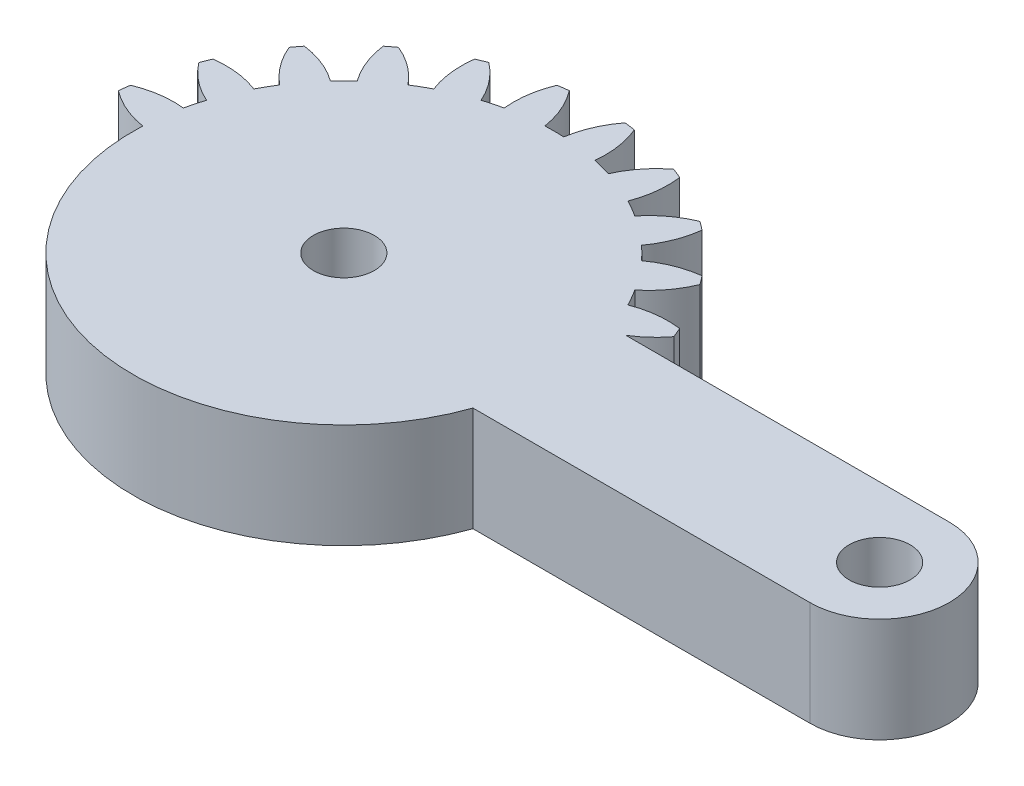
SolidWorks part; units mm, degrees
ref_plane "Front Plane" through (0, 0, 0) normal (0, 0, 1) x (1, 0, 0)
ref_plane "Top Plane" through (0, 0, 0) normal (0, 1, 0) x (1, 0, 0)
ref_plane "Right Plane" through (0, 0, 0) normal (1, 0, 0) x (0, 0, -1)
sketch "Sketch1" plane through (0, 0, 0) normal (0, 1, 0) x (1, 0, 0)
  line L0 (20.6437, 4) -> (2.0816, 4)
  line L1 (2.0816, -4) -> (20.6437, -4)
  arc A0 (2.0816, 4) -> (3.5217, 5.3071) centre (-0.7683, 8.5867) ccw
  arc A1 (3.5217, 5.3071) -> (3.2829, 5.8838) centre (-10.1063, 0) ccw
  arc A2 (3.2829, 5.8838) -> (0.6271, 5.5703) centre (2.5684, 0.5313) ccw
  arc A3 (0.6271, 5.5703) -> (0.0844, 6.5103) centre (-10.1063, 0) ccw
  arc A4 (0.0844, 6.5103) -> (1.6838, 8.6535) centre (-3.3089, 10.711) ccw
  arc A5 (1.6838, 8.6535) -> (1.3038, 9.1487) centre (-10.1063, 0) ccw
  arc A6 (1.3038, 9.1487) -> (-1.1803, 8.1585) centre (1.999, 3.7936) ccw
  arc A7 (-1.1803, 8.1585) -> (-1.9479, 8.926) centre (-10.1063, 0) ccw
  arc A8 (-1.9479, 8.926) -> (-0.9576, 11.4102) centre (-6.3127, 12.1053) ccw
  arc A9 (-0.9576, 11.4102) -> (-1.4528, 11.7901) centre (-10.1063, 0) ccw
  arc A10 (-1.4528, 11.7901) -> (-3.596, 10.1907) centre (0.6046, 6.7975) ccw
  arc A11 (-3.596, 10.1907) -> (-4.5361, 10.7334) centre (-10.1063, 0) ccw
  arc A12 (-4.5361, 10.7334) -> (-4.2225, 13.3892) centre (-9.5751, 12.6747) ccw
  arc A13 (-4.2225, 13.3892) -> (-4.7992, 13.6281) centre (-10.1063, 0) ccw
  arc A14 (-4.7992, 13.6281) -> (-6.4554, 11.5285) centre (-1.5196, 9.3381) ccw
  arc A15 (-6.4554, 11.5285) -> (-7.5039, 11.8094) centre (-10.1063, 0) ccw
  arc A16 (-7.5039, 11.8094) -> (-7.8884, 14.4558) centre (-12.8736, 12.3803) ccw
  arc A17 (-7.8884, 14.4558) -> (-8.5072, 14.5373) centre (-10.1063, 0) ccw
  arc A18 (-8.5072, 14.5373) -> (-9.5636, 12.0806) centre (-4.2291, 11.2423) ccw
  arc A19 (-9.5636, 12.0806) -> (-10.6491, 12.0806) centre (-10.1063, 0) ccw
  arc A20 (-10.6491, 12.0806) -> (-11.7054, 14.5373) centre (-15.9836, 11.2423) ccw
  arc A21 (-11.7054, 14.5373) -> (-12.3243, 14.4558) centre (-10.1063, 0) ccw
  arc A22 (-12.3243, 14.4558) -> (-12.7088, 11.8094) centre (-7.3391, 12.3803) ccw
  arc A23 (-12.7088, 11.8094) -> (-13.7573, 11.5285) centre (-10.1063, 0) ccw
  arc A24 (-13.7573, 11.5285) -> (-15.4135, 13.6281) centre (-18.6931, 9.3381) ccw
  arc A25 (-15.4135, 13.6281) -> (-15.9901, 13.3892) centre (-10.1063, 0) ccw
  arc A26 (-15.9901, 13.3892) -> (-15.6766, 10.7334) centre (-10.6376, 12.6747) ccw
  arc A27 (-15.6766, 10.7334) -> (-16.6166, 10.1907) centre (-10.1063, 0) ccw
  arc A28 (-16.6166, 10.1907) -> (-18.7599, 11.7901) centre (-20.8173, 6.7975) ccw
  arc A29 (-18.7599, 11.7901) -> (-19.255, 11.4102) centre (-10.1063, 0) ccw
  arc A30 (-19.255, 11.4102) -> (-18.2648, 8.926) centre (-13.9, 12.1053) ccw
  arc A31 (-18.2648, 8.926) -> (-19.0324, 8.1585) centre (-10.1063, 0) ccw
  arc A32 (-19.0324, 8.1585) -> (-21.5165, 9.1487) centre (-22.2117, 3.7936) ccw
  arc A33 (-21.5165, 9.1487) -> (-21.8965, 8.6535) centre (-10.1063, 0) ccw
  arc A34 (-21.8965, 8.6535) -> (-20.2971, 6.5103) centre (-16.9038, 10.711) ccw
  arc A35 (-20.2971, 6.5103) -> (-20.8398, 5.5703) centre (-10.1063, 0) ccw
  arc A36 (-20.8398, 5.5703) -> (-23.4956, 5.8838) centre (-22.7811, 0.5313) ccw
  arc A37 (-23.4956, 5.8838) -> (-23.7344, 5.3071) centre (-10.1063, 0) ccw
  arc A38 (-23.7344, 5.3071) -> (-21.6348, 3.6509) centre (-19.4444, 8.5867) ccw
  arc A39 (-21.6348, 3.6509) -> (-21.9157, 2.6025) centre (-10.1063, 0) ccw
  arc A40 (-21.9157, 2.6025) -> (-24.5622, 2.2179) centre (-22.4867, -2.7673) ccw
  arc A41 (-24.5622, 2.2179) -> (-24.6437, 1.5991) centre (-10.1063, 0) ccw
  arc A42 (-24.6437, 1.5991) -> (-22.1869, 0.5427) centre (-21.3486, 5.8773) ccw
  arc A43 (-22.1869, 0.5427) -> (-22.1869, -0.5427) centre (-10.1063, 0) ccw
  arc A44 (-22.1869, -0.5427) -> (-24.6437, -1.5991) centre (-21.3486, -5.8773) ccw
  arc A45 (-24.6437, -1.5991) -> (-24.5622, -2.2179) centre (-10.1063, 0) ccw
  arc A46 (-24.5622, -2.2179) -> (-21.9157, -2.6025) centre (-22.4867, 2.7673) ccw
  arc A47 (-21.9157, -2.6025) -> (-21.6348, -3.6509) centre (-10.1063, 0) ccw
  arc A48 (-21.6348, -3.6509) -> (-23.7344, -5.3071) centre (-19.4444, -8.5867) ccw
  arc A49 (-23.7344, -5.3071) -> (-23.4956, -5.8838) centre (-10.1063, 0) ccw
  arc A50 (-23.4956, -5.8838) -> (-20.8398, -5.5703) centre (-22.7811, -0.5313) ccw
  arc A51 (-20.8398, -5.5703) -> (-20.2971, -6.5103) centre (-10.1063, 0) ccw
  arc A52 (-20.2971, -6.5103) -> (-21.8965, -8.6535) centre (-16.9038, -10.711) ccw
  arc A53 (-21.8965, -8.6535) -> (-21.5165, -9.1487) centre (-10.1063, 0) ccw
  arc A54 (-21.5165, -9.1487) -> (-19.0324, -8.1585) centre (-22.2117, -3.7936) ccw
  arc A55 (-19.0324, -8.1585) -> (-18.2648, -8.926) centre (-10.1063, 0) ccw
  arc A56 (-18.2648, -8.926) -> (-19.255, -11.4102) centre (-13.9, -12.1053) ccw
  arc A57 (-19.255, -11.4102) -> (-18.7599, -11.7901) centre (-10.1063, 0) ccw
  arc A58 (-18.7599, -11.7901) -> (-16.6166, -10.1907) centre (-20.8173, -6.7975) ccw
  arc A59 (-16.6166, -10.1907) -> (-15.6766, -10.7334) centre (-10.1063, 0) ccw
  arc A60 (-15.6766, -10.7334) -> (-15.9901, -13.3892) centre (-10.6376, -12.6747) ccw
  arc A61 (-15.9901, -13.3892) -> (-15.4135, -13.6281) centre (-10.1063, 0) ccw
  arc A62 (-15.4135, -13.6281) -> (-13.7573, -11.5285) centre (-18.6931, -9.3381) ccw
  arc A63 (-13.7573, -11.5285) -> (-12.7088, -11.8094) centre (-10.1063, 0) ccw
  arc A64 (-12.7088, -11.8094) -> (-12.3243, -14.4558) centre (-7.3391, -12.3803) ccw
  arc A65 (-12.3243, -14.4558) -> (-11.7054, -14.5373) centre (-10.1063, 0) ccw
  arc A66 (-11.7054, -14.5373) -> (-10.6491, -12.0806) centre (-15.9836, -11.2423) ccw
  arc A67 (-10.6491, -12.0806) -> (-9.5636, -12.0806) centre (-10.1063, 0) ccw
  arc A68 (-9.5636, -12.0806) -> (-8.5072, -14.5373) centre (-4.2291, -11.2423) ccw
  arc A69 (-8.5072, -14.5373) -> (-7.8884, -14.4558) centre (-10.1063, 0) ccw
  arc A70 (-7.8884, -14.4558) -> (-7.5039, -11.8094) centre (-12.8736, -12.3803) ccw
  arc A71 (-7.5039, -11.8094) -> (-6.4554, -11.5285) centre (-10.1063, 0) ccw
  arc A72 (-6.4554, -11.5285) -> (-4.7992, -13.6281) centre (-1.5196, -9.3381) ccw
  arc A73 (-4.7992, -13.6281) -> (-4.2225, -13.3892) centre (-10.1063, 0) ccw
  arc A74 (-4.2225, -13.3892) -> (-4.5361, -10.7334) centre (-9.5751, -12.6747) ccw
  arc A75 (-4.5361, -10.7334) -> (-3.596, -10.1907) centre (-10.1063, 0) ccw
  arc A76 (-3.596, -10.1907) -> (-1.4528, -11.7901) centre (0.6046, -6.7975) ccw
  arc A77 (-1.4528, -11.7901) -> (-0.9576, -11.4102) centre (-10.1063, 0) ccw
  arc A78 (-0.9576, -11.4102) -> (-1.9479, -8.926) centre (-6.3127, -12.1053) ccw
  arc A79 (-1.9479, -8.926) -> (-1.1803, -8.1585) centre (-10.1063, 0) ccw
  arc A80 (-1.1803, -8.1585) -> (1.3038, -9.1487) centre (1.999, -3.7936) ccw
  arc A81 (1.3038, -9.1487) -> (1.6838, -8.6535) centre (-10.1063, 0) ccw
  arc A82 (1.6838, -8.6535) -> (0.0844, -6.5103) centre (-3.3089, -10.711) ccw
  arc A83 (0.0844, -6.5103) -> (0.6271, -5.5703) centre (-10.1063, 0) ccw
  arc A84 (0.6271, -5.5703) -> (3.2829, -5.8838) centre (2.5684, -0.5313) ccw
  arc A85 (3.2829, -5.8838) -> (3.5217, -5.3071) centre (-10.1063, 0) ccw
  arc A86 (3.5217, -5.3071) -> (2.0816, -4) centre (-0.7683, -8.5867) ccw
  arc A87 (20.6437, -4) -> (20.6437, 4) centre (20.6437, 0) ccw
  circle A88 centre (-10.1063, 0) radius 1.75
  circle A89 centre (20.6437, 0) radius 1.75
  dimension "D1" = 3.5
  dimension "D2" = 3.5
extrude "Boss-Extrude1" add sketch "Sketch1" along normal blind 4
sketch "Sketch2" plane through (0, 4, 0) normal (0, 1, 0) x (1, 0, 0)
  line L0 (2.0816, -4) -> (1.3057, -4)
  line L2 (20.6437, 4) -> (2.0816, 4)
  line L3 (2.0816, -4) -> (20.6437, -4)
  line L4 (20.6437, 4) -> (2.0816, 4)
  line L5 (2.0816, -4) -> (20.6437, -4)
  circle A0 centre (-10.1063, 0) radius 12.0927
  arc A88 (20.6437, -4) -> (20.6437, 4) centre (20.6437, 0) ccw
  arc A89 (2.0816, 4) -> (3.5217, 5.3071) centre (-0.7683, 8.5867) ccw
  arc A90 (3.5217, 5.3071) -> (3.2829, 5.8838) centre (-10.1063, 0) ccw
  arc A91 (3.2829, 5.8838) -> (0.6271, 5.5703) centre (2.5684, 0.5313) ccw
  arc A92 (0.6271, 5.5703) -> (0.0844, 6.5103) centre (-10.1063, 0) ccw
  arc A93 (0.0844, 6.5103) -> (1.6838, 8.6535) centre (-3.3089, 10.711) ccw
  arc A94 (1.6838, 8.6535) -> (1.3038, 9.1487) centre (-10.1063, 0) ccw
  arc A95 (1.3038, 9.1487) -> (-1.1803, 8.1585) centre (1.999, 3.7936) ccw
  arc A96 (-1.1803, 8.1585) -> (-1.9479, 8.926) centre (-10.1063, 0) ccw
  arc A97 (-1.9479, 8.926) -> (-0.9576, 11.4102) centre (-6.3127, 12.1053) ccw
  arc A98 (-0.9576, 11.4102) -> (-1.4528, 11.7901) centre (-10.1063, 0) ccw
  arc A99 (-1.4528, 11.7901) -> (-3.596, 10.1907) centre (0.6046, 6.7975) ccw
  arc A100 (-3.596, 10.1907) -> (-4.5361, 10.7334) centre (-10.1063, 0) ccw
  arc A101 (-4.5361, 10.7334) -> (-4.2225, 13.3892) centre (-9.5751, 12.6747) ccw
  arc A102 (-4.2225, 13.3892) -> (-4.7992, 13.6281) centre (-10.1063, 0) ccw
  arc A103 (-4.7992, 13.6281) -> (-6.4554, 11.5285) centre (-1.5196, 9.3381) ccw
  arc A104 (-6.4554, 11.5285) -> (-7.5039, 11.8094) centre (-10.1063, 0) ccw
  arc A105 (-7.5039, 11.8094) -> (-7.8884, 14.4558) centre (-12.8736, 12.3803) ccw
  arc A106 (-7.8884, 14.4558) -> (-8.5072, 14.5373) centre (-10.1063, 0) ccw
  arc A107 (-8.5072, 14.5373) -> (-9.5636, 12.0806) centre (-4.2291, 11.2423) ccw
  arc A108 (-9.5636, 12.0806) -> (-10.6491, 12.0806) centre (-10.1063, 0) ccw
  arc A109 (-10.6491, 12.0806) -> (-11.7054, 14.5373) centre (-15.9836, 11.2423) ccw
  arc A110 (-11.7054, 14.5373) -> (-12.3243, 14.4558) centre (-10.1063, 0) ccw
  arc A111 (-12.3243, 14.4558) -> (-12.7088, 11.8094) centre (-7.3391, 12.3803) ccw
  arc A112 (-12.7088, 11.8094) -> (-13.7573, 11.5285) centre (-10.1063, 0) ccw
  arc A113 (-13.7573, 11.5285) -> (-15.4135, 13.6281) centre (-18.6931, 9.3381) ccw
  arc A114 (-15.4135, 13.6281) -> (-15.9901, 13.3892) centre (-10.1063, 0) ccw
  arc A115 (-15.9901, 13.3892) -> (-15.6766, 10.7334) centre (-10.6376, 12.6747) ccw
  arc A116 (-15.6766, 10.7334) -> (-16.6166, 10.1907) centre (-10.1063, 0) ccw
  arc A117 (-16.6166, 10.1907) -> (-18.7599, 11.7901) centre (-20.8173, 6.7975) ccw
  arc A118 (-18.7599, 11.7901) -> (-19.255, 11.4102) centre (-10.1063, 0) ccw
  arc A119 (-19.255, 11.4102) -> (-18.2648, 8.926) centre (-13.9, 12.1053) ccw
  arc A120 (-18.2648, 8.926) -> (-19.0324, 8.1585) centre (-10.1063, 0) ccw
  arc A121 (-19.0324, 8.1585) -> (-21.5165, 9.1487) centre (-22.2117, 3.7936) ccw
  arc A122 (-21.5165, 9.1487) -> (-21.8965, 8.6535) centre (-10.1063, 0) ccw
  arc A123 (-21.8965, 8.6535) -> (-20.2971, 6.5103) centre (-16.9038, 10.711) ccw
  arc A124 (-20.2971, 6.5103) -> (-20.8398, 5.5703) centre (-10.1063, 0) ccw
  arc A125 (-20.8398, 5.5703) -> (-23.4956, 5.8838) centre (-22.7811, 0.5313) ccw
  arc A126 (-23.4956, 5.8838) -> (-23.7344, 5.3071) centre (-10.1063, 0) ccw
  arc A127 (-23.7344, 5.3071) -> (-21.6348, 3.6509) centre (-19.4444, 8.5867) ccw
  arc A128 (-21.6348, 3.6509) -> (-21.9157, 2.6025) centre (-10.1063, 0) ccw
  arc A129 (-21.9157, 2.6025) -> (-24.5622, 2.2179) centre (-22.4867, -2.7673) ccw
  arc A130 (-24.5622, 2.2179) -> (-24.6437, 1.5991) centre (-10.1063, 0) ccw
  arc A131 (-24.6437, 1.5991) -> (-22.1869, 0.5427) centre (-21.3486, 5.8773) ccw
  arc A132 (-22.1869, 0.5427) -> (-22.1869, -0.5427) centre (-10.1063, 0) ccw
  arc A133 (-22.1869, -0.5427) -> (-24.6437, -1.5991) centre (-21.3486, -5.8773) ccw
  arc A134 (-24.6437, -1.5991) -> (-24.5622, -2.2179) centre (-10.1063, 0) ccw
  arc A135 (-24.5622, -2.2179) -> (-21.9157, -2.6025) centre (-22.4867, 2.7673) ccw
  arc A136 (-21.9157, -2.6025) -> (-21.6348, -3.6509) centre (-10.1063, 0) ccw
  arc A137 (-21.6348, -3.6509) -> (-23.7344, -5.3071) centre (-19.4444, -8.5867) ccw
  arc A138 (-23.7344, -5.3071) -> (-23.4956, -5.8838) centre (-10.1063, 0) ccw
  arc A139 (-23.4956, -5.8838) -> (-20.8398, -5.5703) centre (-22.7811, -0.5313) ccw
  arc A140 (-20.8398, -5.5703) -> (-20.2971, -6.5103) centre (-10.1063, 0) ccw
  arc A141 (-20.2971, -6.5103) -> (-21.8965, -8.6535) centre (-16.9038, -10.711) ccw
  arc A142 (-21.8965, -8.6535) -> (-21.5165, -9.1487) centre (-10.1063, 0) ccw
  arc A143 (-21.5165, -9.1487) -> (-19.0324, -8.1585) centre (-22.2117, -3.7936) ccw
  arc A144 (-19.0324, -8.1585) -> (-18.2648, -8.926) centre (-10.1063, 0) ccw
  arc A145 (-18.2648, -8.926) -> (-19.255, -11.4102) centre (-13.9, -12.1053) ccw
  arc A146 (-19.255, -11.4102) -> (-18.7599, -11.7901) centre (-10.1063, 0) ccw
  arc A147 (-18.7599, -11.7901) -> (-16.6166, -10.1907) centre (-20.8173, -6.7975) ccw
  arc A148 (-16.6166, -10.1907) -> (-15.6766, -10.7334) centre (-10.1063, 0) ccw
  arc A149 (-15.6766, -10.7334) -> (-15.9901, -13.3892) centre (-10.6376, -12.6747) ccw
  arc A150 (-15.9901, -13.3892) -> (-15.4135, -13.6281) centre (-10.1063, 0) ccw
  arc A151 (-15.4135, -13.6281) -> (-13.7573, -11.5285) centre (-18.6931, -9.3381) ccw
  arc A152 (-13.7573, -11.5285) -> (-12.7088, -11.8094) centre (-10.1063, 0) ccw
  arc A153 (-12.7088, -11.8094) -> (-12.3243, -14.4558) centre (-7.3391, -12.3803) ccw
  arc A154 (-12.3243, -14.4558) -> (-11.7054, -14.5373) centre (-10.1063, 0) ccw
  arc A155 (-11.7054, -14.5373) -> (-10.6491, -12.0806) centre (-15.9836, -11.2423) ccw
  arc A156 (-10.6491, -12.0806) -> (-9.5636, -12.0806) centre (-10.1063, 0) ccw
  arc A157 (-9.5636, -12.0806) -> (-8.5072, -14.5373) centre (-4.2291, -11.2423) ccw
  arc A158 (-8.5072, -14.5373) -> (-7.8884, -14.4558) centre (-10.1063, 0) ccw
  arc A159 (-7.8884, -14.4558) -> (-7.5039, -11.8094) centre (-12.8736, -12.3803) ccw
  arc A160 (-7.5039, -11.8094) -> (-6.4554, -11.5285) centre (-10.1063, 0) ccw
  arc A161 (-6.4554, -11.5285) -> (-4.7992, -13.6281) centre (-1.5196, -9.3381) ccw
  arc A162 (-4.7992, -13.6281) -> (-4.2225, -13.3892) centre (-10.1063, 0) ccw
  arc A163 (-4.2225, -13.3892) -> (-4.5361, -10.7334) centre (-9.5751, -12.6747) ccw
  arc A164 (-4.5361, -10.7334) -> (-3.596, -10.1907) centre (-10.1063, 0) ccw
  arc A165 (-3.596, -10.1907) -> (-1.4528, -11.7901) centre (0.6046, -6.7975) ccw
  arc A166 (-1.4528, -11.7901) -> (-0.9576, -11.4102) centre (-10.1063, 0) ccw
  arc A167 (-0.9576, -11.4102) -> (-1.9479, -8.926) centre (-6.3127, -12.1053) ccw
  arc A168 (-1.9479, -8.926) -> (-1.1803, -8.1585) centre (-10.1063, 0) ccw
  arc A169 (-1.1803, -8.1585) -> (1.3038, -9.1487) centre (1.999, -3.7936) ccw
  arc A170 (1.3038, -9.1487) -> (1.6838, -8.6535) centre (-10.1063, 0) ccw
  arc A171 (1.6838, -8.6535) -> (0.0844, -6.5103) centre (-3.3089, -10.711) ccw
  arc A172 (0.0844, -6.5103) -> (0.6271, -5.5703) centre (-10.1063, 0) ccw
  arc A173 (0.6271, -5.5703) -> (3.2829, -5.8838) centre (2.5684, -0.5313) ccw
  arc A174 (3.2829, -5.8838) -> (3.5217, -5.3071) centre (-10.1063, 0) ccw
  arc A175 (3.5217, -5.3071) -> (2.0816, -4) centre (-0.7683, -8.5867) ccw
  arc A176 (20.6437, -4) -> (20.6437, 4) centre (20.6437, 0) ccw
  arc A177 (2.0816, 4) -> (3.5217, 5.3071) centre (-0.7683, 8.5867) ccw
  arc A178 (3.5217, 5.3071) -> (3.2829, 5.8838) centre (-10.1063, 0) ccw
  arc A179 (3.2829, 5.8838) -> (0.6271, 5.5703) centre (2.5684, 0.5313) ccw
  arc A180 (0.6271, 5.5703) -> (0.0844, 6.5103) centre (-10.1063, 0) ccw
  arc A181 (0.0844, 6.5103) -> (1.6838, 8.6535) centre (-3.3089, 10.711) ccw
  arc A182 (1.6838, 8.6535) -> (1.3038, 9.1487) centre (-10.1063, 0) ccw
  arc A183 (1.3038, 9.1487) -> (-1.1803, 8.1585) centre (1.999, 3.7936) ccw
  arc A184 (-1.1803, 8.1585) -> (-1.9479, 8.926) centre (-10.1063, 0) ccw
  arc A185 (-1.9479, 8.926) -> (-0.9576, 11.4102) centre (-6.3127, 12.1053) ccw
  arc A186 (-0.9576, 11.4102) -> (-1.4528, 11.7901) centre (-10.1063, 0) ccw
  arc A187 (-1.4528, 11.7901) -> (-3.596, 10.1907) centre (0.6046, 6.7975) ccw
  arc A188 (-3.596, 10.1907) -> (-4.5361, 10.7334) centre (-10.1063, 0) ccw
  arc A189 (-4.5361, 10.7334) -> (-4.2225, 13.3892) centre (-9.5751, 12.6747) ccw
  arc A190 (-4.2225, 13.3892) -> (-4.7992, 13.6281) centre (-10.1063, 0) ccw
  arc A191 (-4.7992, 13.6281) -> (-6.4554, 11.5285) centre (-1.5196, 9.3381) ccw
  arc A192 (-6.4554, 11.5285) -> (-7.5039, 11.8094) centre (-10.1063, 0) ccw
  arc A193 (-7.5039, 11.8094) -> (-7.8884, 14.4558) centre (-12.8736, 12.3803) ccw
  arc A194 (-7.8884, 14.4558) -> (-8.5072, 14.5373) centre (-10.1063, 0) ccw
  arc A195 (-8.5072, 14.5373) -> (-9.5636, 12.0806) centre (-4.2291, 11.2423) ccw
  arc A196 (-9.5636, 12.0806) -> (-10.6491, 12.0806) centre (-10.1063, 0) ccw
  arc A197 (-10.6491, 12.0806) -> (-11.7054, 14.5373) centre (-15.9836, 11.2423) ccw
  arc A198 (-11.7054, 14.5373) -> (-12.3243, 14.4558) centre (-10.1063, 0) ccw
  arc A199 (-12.3243, 14.4558) -> (-12.7088, 11.8094) centre (-7.3391, 12.3803) ccw
  arc A200 (-12.7088, 11.8094) -> (-13.7573, 11.5285) centre (-10.1063, 0) ccw
  arc A201 (-13.7573, 11.5285) -> (-15.4135, 13.6281) centre (-18.6931, 9.3381) ccw
  arc A202 (-15.4135, 13.6281) -> (-15.9901, 13.3892) centre (-10.1063, 0) ccw
  arc A203 (-15.9901, 13.3892) -> (-15.6766, 10.7334) centre (-10.6376, 12.6747) ccw
  arc A204 (-15.6766, 10.7334) -> (-16.6166, 10.1907) centre (-10.1063, 0) ccw
  arc A205 (-16.6166, 10.1907) -> (-18.7599, 11.7901) centre (-20.8173, 6.7975) ccw
  arc A206 (-18.7599, 11.7901) -> (-19.255, 11.4102) centre (-10.1063, 0) ccw
  arc A207 (-19.255, 11.4102) -> (-18.2648, 8.926) centre (-13.9, 12.1053) ccw
  arc A208 (-18.2648, 8.926) -> (-19.0324, 8.1585) centre (-10.1063, 0) ccw
  arc A209 (-19.0324, 8.1585) -> (-21.5165, 9.1487) centre (-22.2117, 3.7936) ccw
  arc A210 (-21.5165, 9.1487) -> (-21.8965, 8.6535) centre (-10.1063, 0) ccw
  arc A211 (-21.8965, 8.6535) -> (-20.2971, 6.5103) centre (-16.9038, 10.711) ccw
  arc A212 (-20.2971, 6.5103) -> (-20.8398, 5.5703) centre (-10.1063, 0) ccw
  arc A213 (-20.8398, 5.5703) -> (-23.4956, 5.8838) centre (-22.7811, 0.5313) ccw
  arc A214 (-23.4956, 5.8838) -> (-23.7344, 5.3071) centre (-10.1063, 0) ccw
  arc A215 (-23.7344, 5.3071) -> (-21.6348, 3.6509) centre (-19.4444, 8.5867) ccw
  arc A216 (-21.6348, 3.6509) -> (-21.9157, 2.6025) centre (-10.1063, 0) ccw
  arc A217 (-21.9157, 2.6025) -> (-24.5622, 2.2179) centre (-22.4867, -2.7673) ccw
  arc A218 (-24.5622, 2.2179) -> (-24.6437, 1.5991) centre (-10.1063, 0) ccw
  arc A219 (-24.6437, 1.5991) -> (-22.1869, 0.5427) centre (-21.3486, 5.8773) ccw
  arc A220 (-22.1869, 0.5427) -> (-22.1869, -0.5427) centre (-10.1063, 0) ccw
  arc A221 (-22.1869, -0.5427) -> (-24.6437, -1.5991) centre (-21.3486, -5.8773) ccw
  arc A222 (-24.6437, -1.5991) -> (-24.5622, -2.2179) centre (-10.1063, 0) ccw
  arc A223 (-24.5622, -2.2179) -> (-21.9157, -2.6025) centre (-22.4867, 2.7673) ccw
  arc A224 (-21.9157, -2.6025) -> (-21.6348, -3.6509) centre (-10.1063, 0) ccw
  arc A225 (-21.6348, -3.6509) -> (-23.7344, -5.3071) centre (-19.4444, -8.5867) ccw
  arc A226 (-23.7344, -5.3071) -> (-23.4956, -5.8838) centre (-10.1063, 0) ccw
  arc A227 (-23.4956, -5.8838) -> (-20.8398, -5.5703) centre (-22.7811, -0.5313) ccw
  arc A228 (-20.8398, -5.5703) -> (-20.2971, -6.5103) centre (-10.1063, 0) ccw
  arc A229 (-20.2971, -6.5103) -> (-21.8965, -8.6535) centre (-16.9038, -10.711) ccw
  arc A230 (-21.8965, -8.6535) -> (-21.5165, -9.1487) centre (-10.1063, 0) ccw
  arc A231 (-21.5165, -9.1487) -> (-19.0324, -8.1585) centre (-22.2117, -3.7936) ccw
  arc A232 (-19.0324, -8.1585) -> (-18.2648, -8.926) centre (-10.1063, 0) ccw
  arc A233 (-18.2648, -8.926) -> (-19.255, -11.4102) centre (-13.9, -12.1053) ccw
  arc A234 (-19.255, -11.4102) -> (-18.7599, -11.7901) centre (-10.1063, 0) ccw
  arc A235 (-18.7599, -11.7901) -> (-16.6166, -10.1907) centre (-20.8173, -6.7975) ccw
  arc A236 (-16.6166, -10.1907) -> (-15.6766, -10.7334) centre (-10.1063, 0) ccw
  arc A237 (-15.6766, -10.7334) -> (-15.9901, -13.3892) centre (-10.6376, -12.6747) ccw
  arc A238 (-15.9901, -13.3892) -> (-15.4135, -13.6281) centre (-10.1063, 0) ccw
  arc A239 (-15.4135, -13.6281) -> (-13.7573, -11.5285) centre (-18.6931, -9.3381) ccw
  arc A240 (-13.7573, -11.5285) -> (-12.7088, -11.8094) centre (-10.1063, 0) ccw
  arc A241 (-12.7088, -11.8094) -> (-12.3243, -14.4558) centre (-7.3391, -12.3803) ccw
  arc A242 (-12.3243, -14.4558) -> (-11.7054, -14.5373) centre (-10.1063, 0) ccw
  arc A243 (-11.7054, -14.5373) -> (-10.6491, -12.0806) centre (-15.9836, -11.2423) ccw
  arc A244 (-10.6491, -12.0806) -> (-9.5636, -12.0806) centre (-10.1063, 0) ccw
  arc A245 (-9.5636, -12.0806) -> (-8.5072, -14.5373) centre (-4.2291, -11.2423) ccw
  arc A246 (-8.5072, -14.5373) -> (-7.8884, -14.4558) centre (-10.1063, 0) ccw
  arc A247 (-7.8884, -14.4558) -> (-7.5039, -11.8094) centre (-12.8736, -12.3803) ccw
  arc A248 (-7.5039, -11.8094) -> (-6.4554, -11.5285) centre (-10.1063, 0) ccw
  arc A249 (-6.4554, -11.5285) -> (-4.7992, -13.6281) centre (-1.5196, -9.3381) ccw
  arc A250 (-4.7992, -13.6281) -> (-4.2225, -13.3892) centre (-10.1063, 0) ccw
  arc A251 (-4.2225, -13.3892) -> (-4.5361, -10.7334) centre (-9.5751, -12.6747) ccw
  arc A252 (-4.5361, -10.7334) -> (-3.596, -10.1907) centre (-10.1063, 0) ccw
  arc A253 (-3.596, -10.1907) -> (-1.4528, -11.7901) centre (0.6046, -6.7975) ccw
  arc A254 (-1.4528, -11.7901) -> (-0.9576, -11.4102) centre (-10.1063, 0) ccw
  arc A255 (-0.9576, -11.4102) -> (-1.9479, -8.926) centre (-6.3127, -12.1053) ccw
  arc A256 (-1.9479, -8.926) -> (-1.1803, -8.1585) centre (-10.1063, 0) ccw
  arc A257 (-1.1803, -8.1585) -> (1.3038, -9.1487) centre (1.999, -3.7936) ccw
  arc A258 (1.3038, -9.1487) -> (1.6838, -8.6535) centre (-10.1063, 0) ccw
  arc A259 (1.6838, -8.6535) -> (0.0844, -6.5103) centre (-3.3089, -10.711) ccw
  arc A260 (0.0844, -6.5103) -> (0.6271, -5.5703) centre (-10.1063, 0) ccw
  arc A261 (0.6271, -5.5703) -> (3.2829, -5.8838) centre (2.5684, -0.5313) ccw
  arc A262 (3.2829, -5.8838) -> (3.5217, -5.3071) centre (-10.1063, 0) ccw
  arc A263 (3.5217, -5.3071) -> (2.0816, -4) centre (-0.7683, -8.5867) ccw
  dimension "D1" = 0
extrude "Cut-Extrude1" cut sketch "Sketch2" against normal blind 10 contours A222 A223 A0 A221 | A226 A227 A0 A225 | A230 A231 A0 A229 | A234 A235 A0 A233 | A238 A239 A0 A237 | A242 A243 A0 A241 | A246 A247 A0 A245 | A250 A251 A0 A249 | A254 A255 A0 A253 | A258 A259 A0 A257 | A262 A263 L0 A0 A261
other "Move Face1" face at (20.6437, 0, 1.75) parameters "D1"=2
sketch "Sketch3" plane through (0, 4, 0) normal (0, 1, 0) x (1, 0, 0)
  circle A0 centre (-10.1063, 0) radius 13.45 construction
  circle A1 centre (-10.1063, 0) radius 13.45
